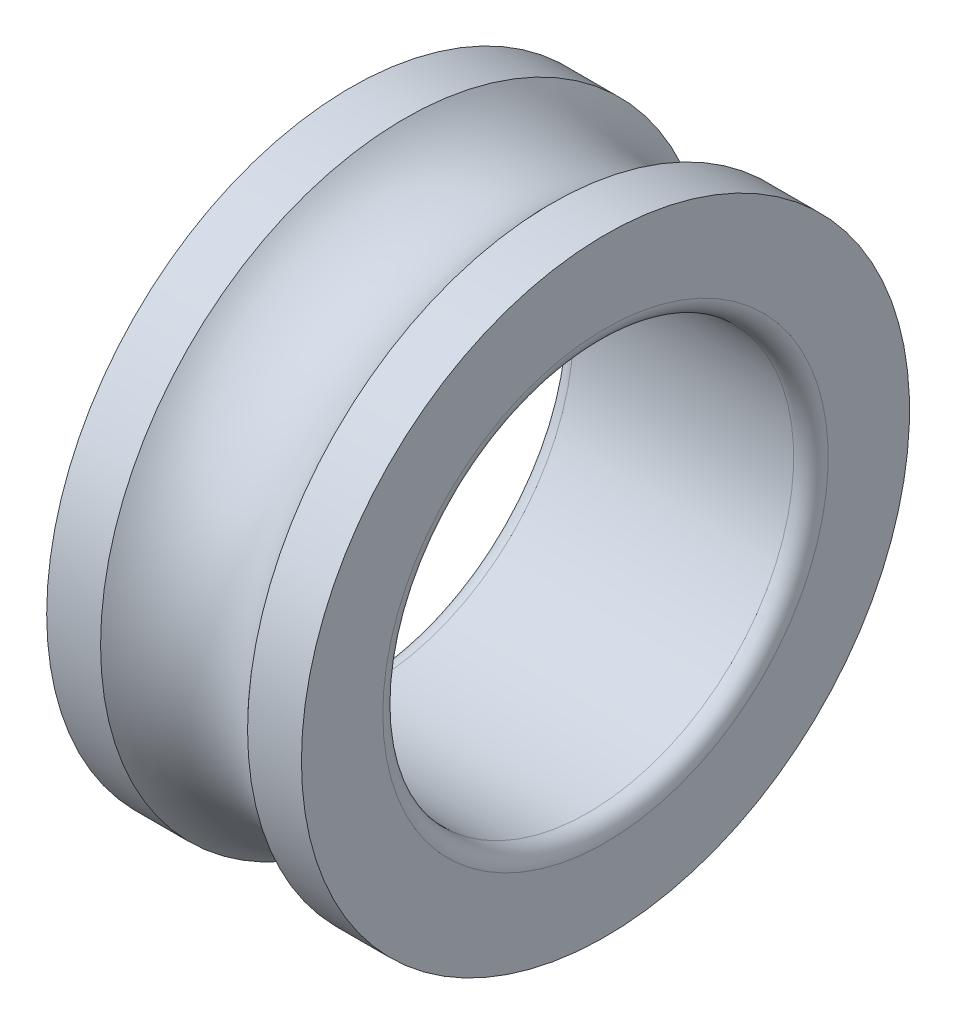
SolidWorks part; units mm, degrees
ref_plane "Front Plane" through (0, 0, 0) normal (0, 0, 1) x (1, 0, 0)
ref_plane "Top Plane" through (0, 0, 0) normal (0, 1, 0) x (1, 0, 0)
ref_plane "Right Plane" through (0, 0, 0) normal (1, 0, 0) x (0, 0, -1)
sketch "Sketch1" plane through (0, 0, 0) normal (0, 0, 1) x (1, 0, 0)
  line L0 (-23.4552, 0) -> (35.3248, 0) construction
  line L1 (0, 25) -> (0, 0) construction
  line L2 (-15.5, 37) -> (-8.9443, 37)
  line L3 (-15.5, 37) -> (-15.5, 27.1)
  line L4 (-13.4, 25) -> (13.4, 25)
  line L5 (15.5, 37) -> (15.5, 27.1)
  line L6 (-15.5, 37) -> (15.5, 25) construction
  line L7 (-15.5, 25) -> (15.5, 37) construction
  line L8 (8.9443, 37) -> (15.5, 37)
  arc A0 (8.9443, 37) -> (-8.9443, 37) centre (0, 45) cw
  arc A1 (13.4, 25) -> (15.5, 27.1) centre (13.4, 27.1) ccw
  arc A2 (-15.5, 27.1) -> (-13.4, 25) centre (-13.4, 27.1) ccw
  point P3 (0, 31)
  dimension "D5" = 12
  dimension "D6" = 2.1
  dimension "D1" = 31
  dimension "D2" = 25
  dimension "D3" = 37
  dimension "D4" = 8
revolve "Revolve1" add sketch "Sketch1" angle 360 about L0
